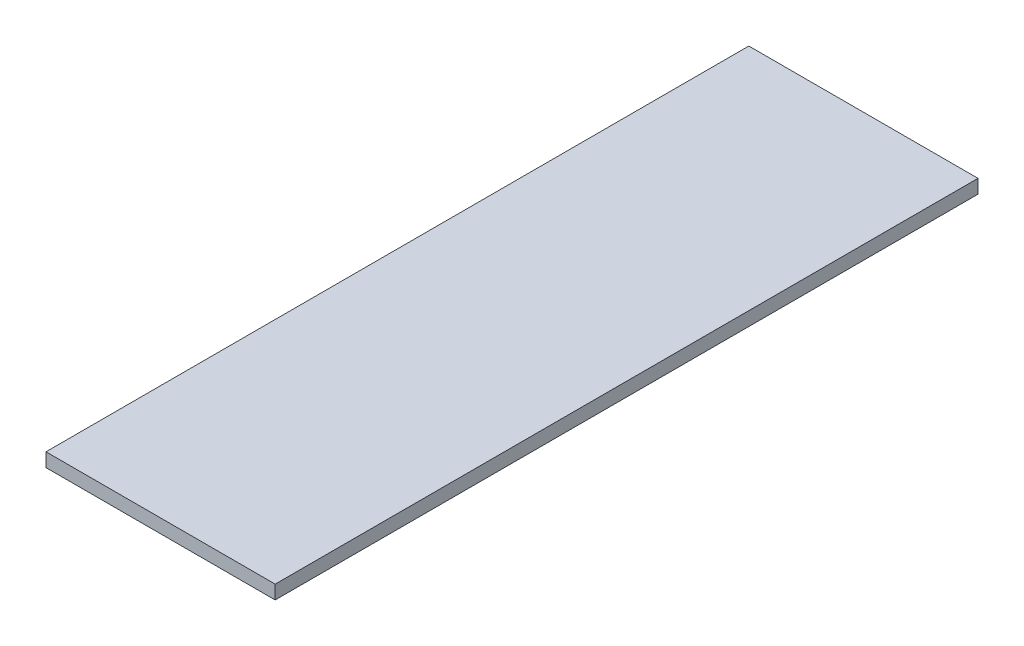
SolidWorks part; units mm, degrees
ref_plane "Спереди" through (0, 0, 0) normal (0, 0, 1) x (1, 0, 0)
ref_plane "Сверху" through (0, 0, 0) normal (0, 1, 0) x (1, 0, 0)
ref_plane "Справа" through (0, 0, 0) normal (1, 0, 0) x (0, 0, -1)
sketch "Эскиз1" plane through (0, 0, 0) normal (0, 1, 0) x (1, 0, 0)
  line L1 (150, -460) -> (-150, -460)
  line L2 (150, -460) -> (150, 460)
  line L3 (150, 460) -> (-150, 460)
  line L4 (-150, -460) -> (-150, 460)
  line L5 (150, -460) -> (-150, 460) construction
  line L6 (150, 460) -> (-150, -460) construction
  point P0 (0, 0)
  dimension "D1" = 300
  dimension "D2" = 920
extrude "Бобышка-Вытянуть1" add sketch "Эскиз1" along normal blind 18
